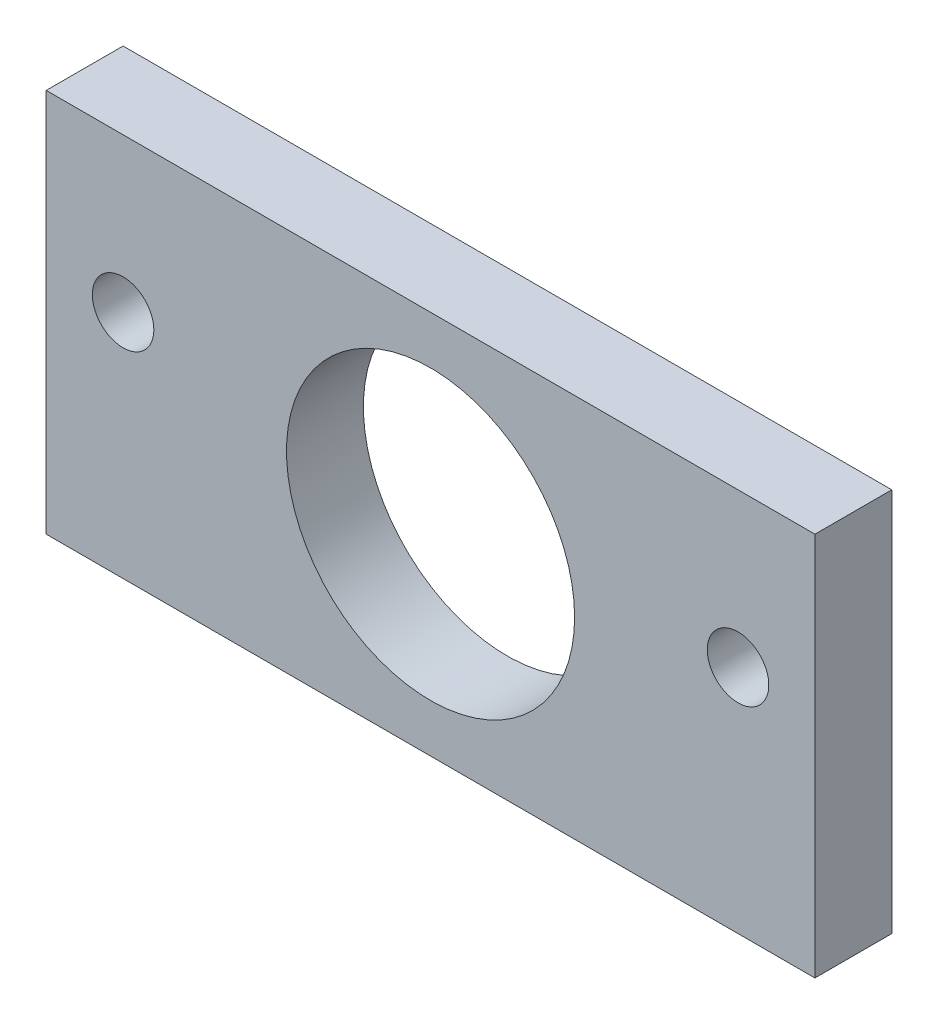
SolidWorks part; units mm, degrees
material "ABS"
ref_plane "Front Plane" through (0, 0, 0) normal (0, 0, 1) x (1, 0, 0)
ref_plane "Top Plane" through (0, 0, 0) normal (0, 1, 0) x (1, 0, 0)
ref_plane "Right Plane" through (0, 0, 0) normal (1, 0, 0) x (0, 0, -1)
sketch "Sketch1" plane through (0, 0, 0) normal (0, 0, 1) x (1, 0, 0)
  line L0 (0, 31.75) -> (63.5, 0) construction
  line L1 (0, 0) -> (63.5, 0)
  line L2 (0, 0) -> (0, 31.75)
  line L3 (0, 31.75) -> (63.5, 31.75)
  line L4 (63.5, 0) -> (63.5, 31.75)
  line L5 (0, 6.35) -> (18.8069, 6.35) construction
  line L12 (6.35, 6.35) -> (6.35, 31.75) construction
  line L14 (31.75, 31.75) -> (31.75, 0) construction
  circle A0 centre (31.75, 15.875) radius 11.8999
  circle A1 centre (6.35, 19.05) radius 2.54
  circle A2 centre (57.15, 19.05) radius 2.54
  point P5 (31.75, 15.875)
  point P23 (6.35, 19.05)
  dimension "D5" = 63.5
  dimension "D2" = 5.08
  dimension "D1" = 23.7998
  dimension "D3" = 31.75
  dimension "D4" = 6.35
  dimension "D6" = 6.35
extrude "Boss-Extrude1" add sketch "Sketch1" along normal blind 6.35
equation "\"base length\" = 21"
equation "\"glass pane length\" = 14.125"
equation "\"glass pane width\" = 10.1875"
equation "\"glass pane wall width\" = 3/4"
equation "\"glass lip\" = 1/4"
equation "\"bolt diameter\" = 0.2"
equation "\"stepper body width\" = 2.22"
equation "\"stepper mount offset\" = 0.19"
equation "\"stepper mount diameter\" = 0.19"
equation "\"stepper shaft offset from body\" = 0.79"
equation "\"stepper spacer thickness\" = 0.2"
equation "\"y axis stepper wall height off base\" = 8"
equation "\"y axis stepper wall bracket thickness\" = 1"
equation "\"y axis stepper wall mount side offset\" = 1/2"
equation "\"y axis stepper wall mount top offset\" = 1/2"
equation "\"y axis stepper wall width\" = \"stepper body width\" + 1                  "
equation "\"thin metal\" = 0.12"
equation "\"thick metal\" = 0.25"
equation "\"foot diameter\"= 0.2"
equation "\"foot inset from corner\"= 1"
equation "\"D1@Boss-Extrude1\" = \"thick metal\""
equation "\"recognizer width\" = 2.5"
equation "\"recognizer nut plate height\" = 1.25"
equation "\"recognizer nut plate offset\" = 1.5"
equation "\"D2@Sketch1\"=\"bolt diameter\""
equation "\"D3@Sketch1\"=\"recognizer nut plate height\""
equation "\"D6@Sketch1\"=0.5/2"
equation "\"D4@Sketch1\"=\"thick metal\""
